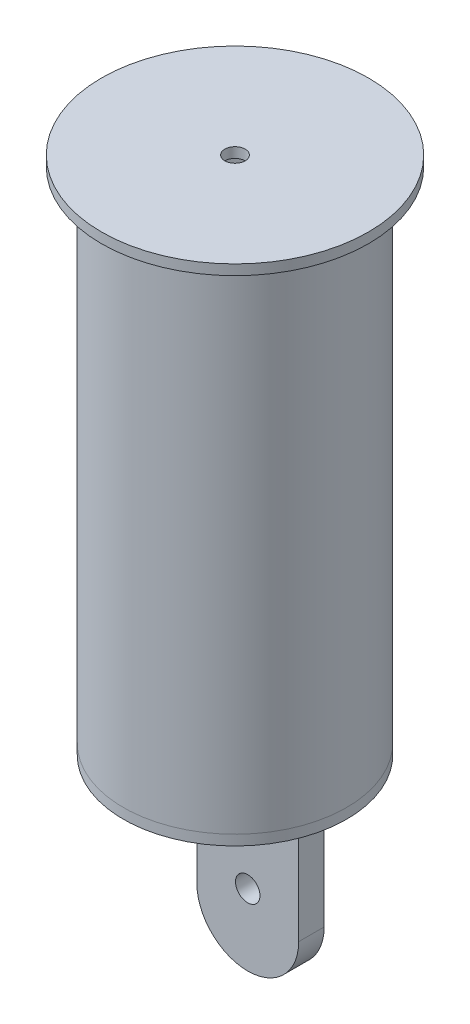
SolidWorks part; units mm, degrees
material "AISI 1020"
ref_plane "Plano frontal" through (0, 0, 0) normal (0, 0, 1) x (1, 0, 0)
ref_plane "Plano superior" through (0, 0, 0) normal (0, 1, 0) x (1, 0, 0)
ref_plane "Plano direito" through (0, 0, 0) normal (1, 0, 0) x (0, 0, -1)
sketch "Esboço1" plane through (0, 0, 0) normal (0, 0, 1) x (1, 0, 0)
  line L0 (0, 0) -> (0, 500) construction
  line L1 (0, 0) -> (215.8131, 0) construction
  line L2 (10, 500) -> (131, 500)
  line L3 (131, 500) -> (131, 490)
  line L4 (103.54, 0) -> (109.54, 0)
  line L7 (103.54, 0) -> (103.54, 490)
  line L8 (103.54, 490) -> (10, 490)
  line L10 (131, 490) -> (109.54, 490)
  line L11 (109.54, 490) -> (109.54, 0)
  line L12 (10, 500) -> (10, 490)
  dimension "D1" = 6
  dimension "D2" = 10
  dimension "D5" = 262
  dimension "D6" = 490
  dimension "D7" = 219.08
  dimension "D8" = 20
revolve "Revolução1" add sketch "Esboço1" angle 360 about L0
sketch "Esboço3" plane through (0, 0, 0) normal (0, -1, 0) x (1, 0, 0)
  circle A1 centre (0, 0) radius 109.54
  circle A2 centre (0, 0) radius 109.54 construction
extrude "Ressalto-extrusão1" add sketch "Esboço3" along normal blind 10 separate body
sketch "Esboço4" plane through (0, 0, 0) normal (0, 0, 1) x (1, 0, 0)
  line L0 (0, -10) -> (0, -299.7341) construction
  line L2 (-50, -10) -> (-50, -150)
  line L3 (-50, -10) -> (50, -10)
  line L4 (50, -10) -> (50, -150)
  line L5 (-109.54, -10) -> (109.54, -10) construction
  arc A0 (-50, -150) -> (50, -150) centre (0, -150) ccw
  circle A1 centre (0, -130) radius 12
  dimension "D1" = 24
  dimension "D2" = 100
  dimension "D3" = 120
  dimension "D4" = 140
extrude "Ressalto-extrusão2" add sketch "Esboço4" against normal blind 25 from offset 12.5
